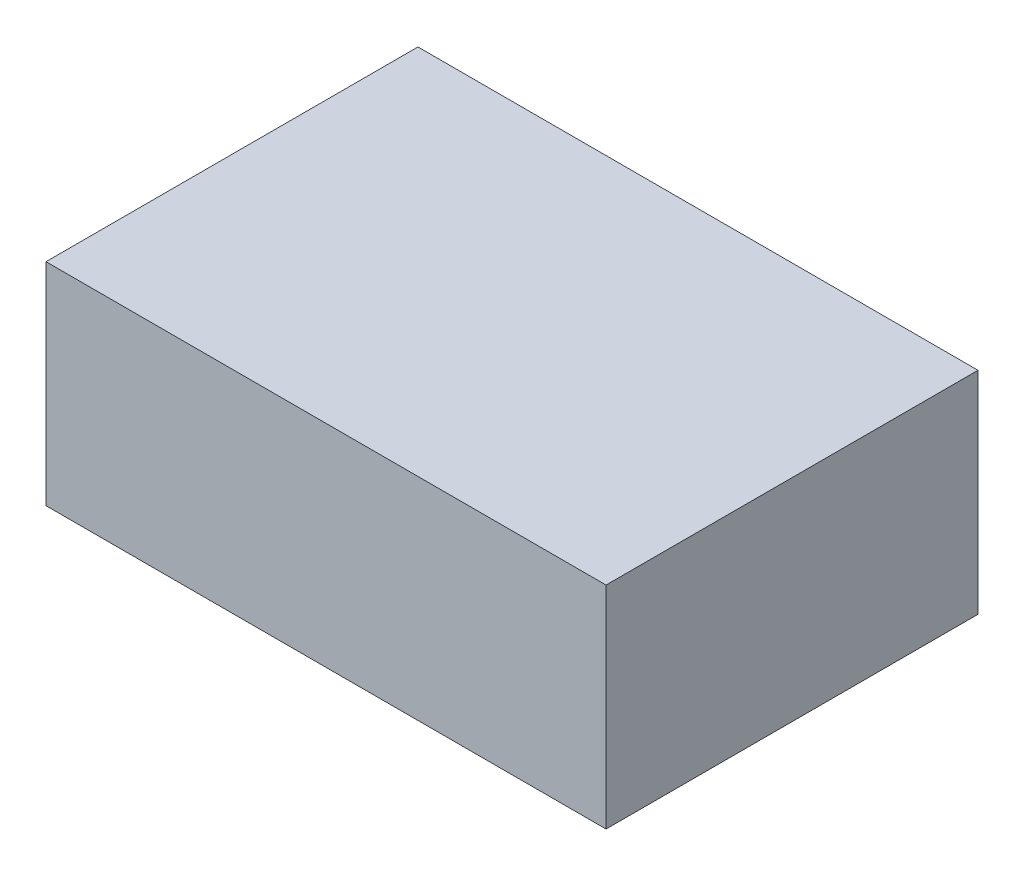
SolidWorks part; units mm, degrees
ref_plane "Front Plane" through (0, 0, 0) normal (0, 0, 1) x (1, 0, 0)
ref_plane "Top Plane" through (0, 0, 0) normal (0, 1, 0) x (1, 0, 0)
ref_plane "Right Plane" through (0, 0, 0) normal (1, 0, 0) x (0, 0, -1)
sketch "Sketch1" plane through (0, 0, 0) normal (0, 1, 0) x (1, 0, 0)
  line L1 (15.2482, 39.7339) -> (41.7482, 39.7339)
  line L2 (15.2482, 39.7339) -> (15.2482, 22.1339)
  line L3 (15.2482, 22.1339) -> (41.7482, 22.1339)
  line L4 (41.7482, 39.7339) -> (41.7482, 22.1339)
  line L5 (15.2482, 39.7339) -> (41.7482, 22.1339) construction
  line L6 (15.2482, 22.1339) -> (41.7482, 39.7339) construction
  point P0 (28.4982, 30.9339)
  dimension "D1" = 17.6
  dimension "D2" = 26.5
extrude "Boss-Extrude1" add sketch "Sketch1" along normal blind 10
